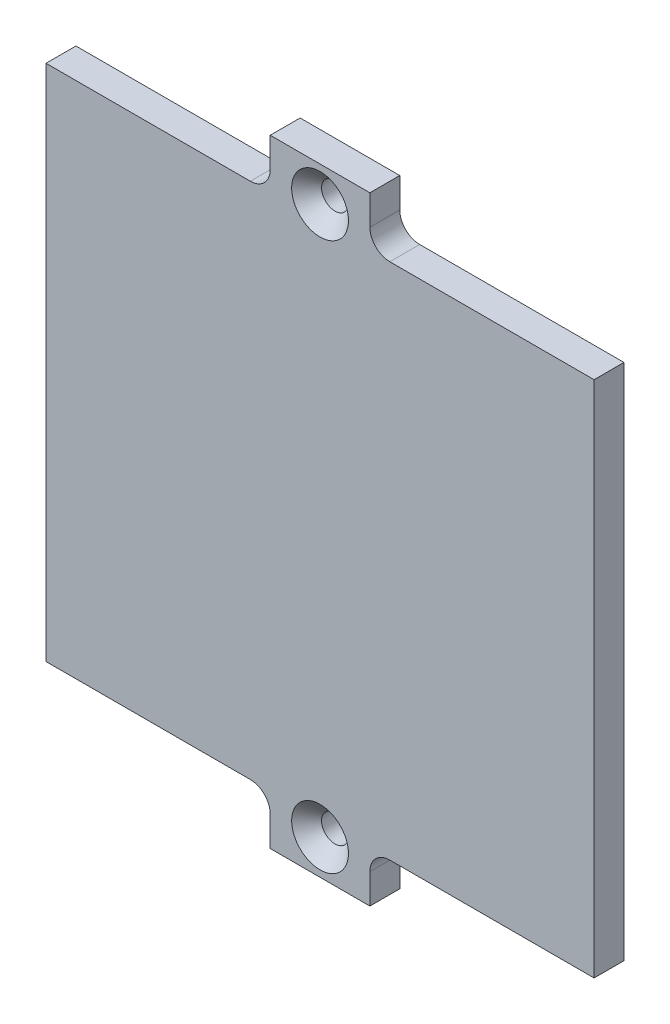
SolidWorks part; units mm, degrees
ref_plane "Front" through (0, 0, 0) normal (0, 0, 1) x (1, 0, 0)
ref_plane "Top" through (0, 0, 0) normal (0, 1, 0) x (1, 0, 0)
ref_plane "Right" through (0, 0, 0) normal (1, 0, 0) x (0, 0, -1)
sketch "Эскиз1" plane through (0, 0, 0) normal (0, 0, 1) x (1, 0, 0)
  line L0 (68.8, -11.45) -> (68.8, 11.15)
  line L26 (66.6, -11.45) -> (66.6, -11.3)
  line L27 (66.6, -11.3) -> (62.8, -11.3)
  line L28 (62.8, -11.3) -> (62.8, -13.2)
  line L29 (65.8, -17.073) -> (65.8, -21.15)
  line L30 (63.8, -23.15) -> (18.8, -23.15)
  line L31 (16.8, -21.15) -> (16.8, 20.85)
  line L32 (18.8, 22.85) -> (63.8, 22.85)
  line L33 (65.8, 20.85) -> (65.8, 16.773)
  line L34 (62.8, 12.9) -> (62.8, 11)
  line L35 (62.8, 11) -> (66.6, 11)
  line L36 (66.6, 11) -> (66.6, 11.15)
  line L37 (66.6, 11.15) -> (68.8, 11.15)
  line L38 (68.8, 11.15) -> (68.8, 25.85)
  line L39 (68.8, 25.85) -> (48.3, 25.85)
  line L40 (46.3, 27.85) -> (46.3, 30.8449)
  line L41 (46.3, 30.8449) -> (36.3, 30.8449)
  line L42 (36.3, 30.8449) -> (36.3, 27.85)
  line L43 (34.3, 25.85) -> (13.8, 25.85)
  line L44 (13.8, 25.85) -> (13.8, -26.15)
  line L45 (13.8, -26.15) -> (34.3, -26.15)
  line L46 (36.3, -28.15) -> (36.3, -31.15)
  line L47 (36.3, -31.15) -> (46.3, -31.15)
  line L48 (46.3, -31.15) -> (46.3, -28.15)
  line L49 (48.3, -26.15) -> (68.8, -26.15)
  line L50 (68.8, -26.15) -> (68.8, -11.45)
  line L51 (68.8, -11.45) -> (66.6, -11.45)
  line L52 (66.6, -11.45) -> (66.6, -11.3)
  line L53 (66.6, -11.3) -> (62.8, -11.3)
  line L54 (62.8, -11.3) -> (62.8, -13.2)
  line L55 (65.8, -17.073) -> (65.8, -21.15)
  line L56 (63.8, -23.15) -> (18.8, -23.15)
  line L57 (16.8, -21.15) -> (16.8, 20.85)
  line L58 (18.8, 22.85) -> (63.8, 22.85)
  line L59 (65.8, 20.85) -> (65.8, 16.773)
  line L60 (62.8, 12.9) -> (62.8, 11)
  line L61 (62.8, 11) -> (66.6, 11)
  line L62 (66.6, 11) -> (66.6, 11.15)
  line L63 (66.6, 11.15) -> (68.8, 11.15)
  line L64 (68.8, 11.15) -> (68.8, 25.85)
  line L65 (68.8, 25.85) -> (48.3, 25.85)
  line L66 (46.3, 27.85) -> (46.3, 30.8449)
  line L67 (46.3, 30.8449) -> (36.3, 30.8449)
  line L68 (36.3, 30.8449) -> (36.3, 27.85)
  line L69 (34.3, 25.85) -> (13.8, 25.85)
  line L70 (13.8, 25.85) -> (13.8, -26.15)
  line L71 (13.8, -26.15) -> (34.3, -26.15)
  line L72 (36.3, -28.15) -> (36.3, -31.15)
  line L73 (36.3, -31.15) -> (46.3, -31.15)
  line L74 (46.3, -31.15) -> (46.3, -28.15)
  line L75 (48.3, -26.15) -> (68.8, -26.15)
  line L76 (68.8, -26.15) -> (68.8, -11.45)
  line L77 (68.8, -11.45) -> (66.6, -11.45)
  circle A1 centre (41.3, 27.3475) radius 1.35
  circle A2 centre (41.3, 27.3475) radius 1.35
  circle A3 centre (41.3, -27.6525) radius 1.35
  circle A4 centre (41.3, -27.6525) radius 1.35
  arc A10 (65.8, -17.073) -> (62.8, -13.2) centre (61.8, -17.073) ccw
  arc A11 (63.8, -23.15) -> (65.8, -21.15) centre (63.8, -21.15) ccw
  arc A12 (16.8, -21.15) -> (18.8, -23.15) centre (18.8, -21.15) ccw
  arc A13 (18.8, 22.85) -> (16.8, 20.85) centre (18.8, 20.85) ccw
  arc A14 (65.8, 20.85) -> (63.8, 22.85) centre (63.8, 20.85) ccw
  arc A15 (62.8, 12.9) -> (65.8, 16.773) centre (61.8, 16.773) ccw
  arc A16 (46.3, 27.85) -> (48.3, 25.85) centre (48.3, 27.85) ccw
  arc A17 (34.3, 25.85) -> (36.3, 27.85) centre (34.3, 27.85) ccw
  arc A18 (36.3, -28.15) -> (34.3, -26.15) centre (34.3, -28.15) ccw
  arc A19 (48.3, -26.15) -> (46.3, -28.15) centre (48.3, -28.15) ccw
  arc A20 (65.8, -17.073) -> (62.8, -13.2) centre (61.8, -17.073) ccw
  arc A21 (63.8, -23.15) -> (65.8, -21.15) centre (63.8, -21.15) ccw
  arc A22 (16.8, -21.15) -> (18.8, -23.15) centre (18.8, -21.15) ccw
  arc A23 (18.8, 22.85) -> (16.8, 20.85) centre (18.8, 20.85) ccw
  arc A24 (65.8, 20.85) -> (63.8, 22.85) centre (63.8, 20.85) ccw
  arc A25 (62.8, 12.9) -> (65.8, 16.773) centre (61.8, 16.773) ccw
  arc A26 (46.3, 27.85) -> (48.3, 25.85) centre (48.3, 27.85) ccw
  arc A27 (34.3, 25.85) -> (36.3, 27.85) centre (34.3, 27.85) ccw
  arc A28 (36.3, -28.15) -> (34.3, -26.15) centre (34.3, -28.15) ccw
  arc A29 (48.3, -26.15) -> (46.3, -28.15) centre (48.3, -28.15) ccw
  dimension "D1" = 0
  dimension "D2" = 0
  dimension "D3" = 0
extrude "Бобышка-Вытянуть1" add sketch "Эскиз1" along normal blind 3 contours A29 L75 L76 L77 L52 L53 L54 A20 L55 A21 L56 A22 L57 A23 L58 A24 L59 A25 L60 L61 L62 L63 L64 L65 A26 L66 L67 L68 A27 L69 L70 L71 A28 L72 L73 L74 | L60 A25 L59 A24 L58 A23 L57 A22 L56 A21 L55 A20 L54 L53 L52 L77 L0 L63 L62 L61
chamfer "Фаска1" distance 1.5 angle 45 2 edges at (42.65, 27.3475, 3) (42.65, -27.6525, 3)
